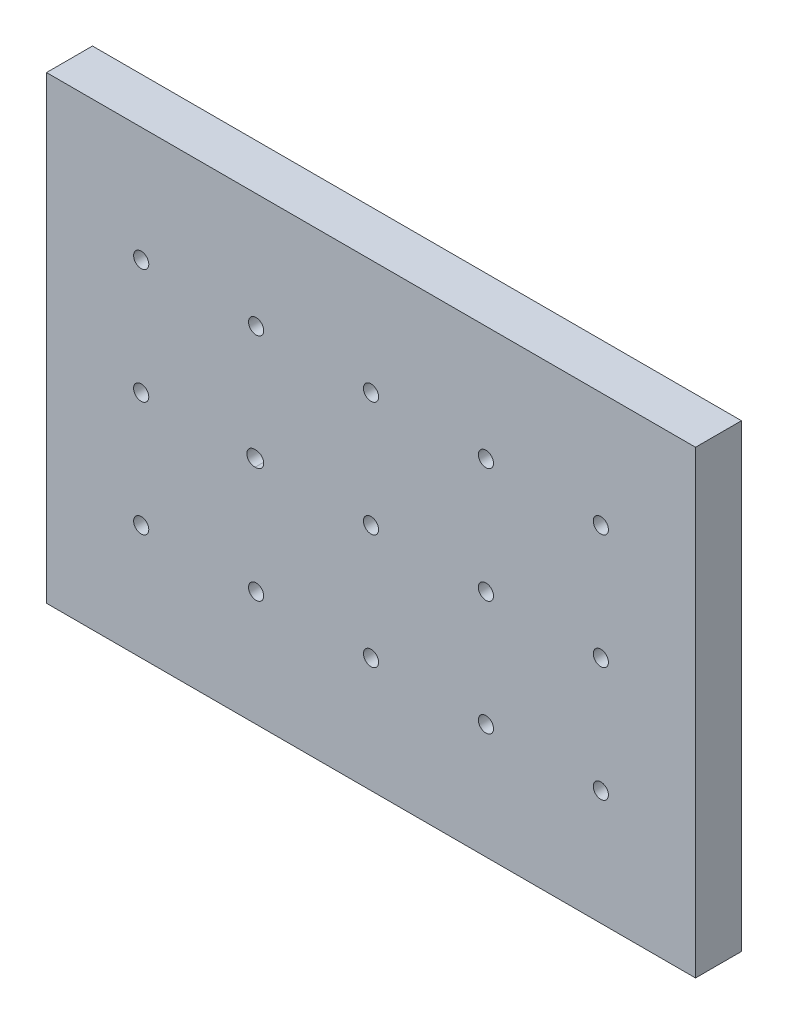
SolidWorks part; units mm, degrees
ref_plane "Front Plane" through (0, 0, 0) normal (0, 0, 1) x (1, 0, 0)
ref_plane "Top Plane" through (0, 0, 0) normal (0, 1, 0) x (1, 0, 0)
ref_plane "Right Plane" through (0, 0, 0) normal (1, 0, 0) x (0, 0, -1)
sketch "Sketch1" plane through (0, 0, 0) normal (0, 0, 1) x (1, 0, 0)
  line L1 (0, 0) -> (-141.2, 0)
  line L2 (0, 0) -> (0, 100)
  line L3 (0, 100) -> (-141.2, 100)
  line L4 (-141.2, 0) -> (-141.2, 100)
  dimension "D1" = 100
  dimension "D2" = 141.2
extrude "Boss-Extrude1" add sketch "Sketch1" along normal blind 10
hole_wizard "M4x0.7 Tapped Hole1" positions "Sketch2" profile "Sketch3" tap size "M4x0.7" standard "ANSI Metric" end condition through all
sketch "Sketch2" plane through (0, 0, 10) normal (0, 0, 1) x (1, 0, 0)
  line L0 (-141.2, 50) -> (0, 50) construction
  line L1 (-141.2, 100) -> (-141.2, 0) construction
  line L2 (0, 0) -> (0, 100) construction
  line L3 (-141.2, 100) -> (-141.2, 0) construction
  line L4 (-141.2, 62.5) -> (0, 62.5) construction
  line L6 (-141.2, 37.5) -> (0, 37.5) construction
  point P9 (-70.6, 50)
  point P10 (-95.6, 50)
  point P12 (-20.6, 50)
  point P14 (-45.6, 50)
  point P18 (-95.9728, 50)
  point P20 (-120.6, 50)
  point P43 (-20.6, 25)
  point P44 (-45.6, 25)
  point P45 (-70.6, 25)
  point P46 (-95.6, 25)
  point P47 (-120.6, 25)
  point P48 (-20.6, 75)
  point P49 (-45.6, 75)
  point P50 (-70.6, 75)
  point P51 (-95.6, 75)
  point P52 (-120.6, 75)
  dimension "D1" = 25
  dimension "D2" = 25
  dimension "D3" = 25
  dimension "D4" = 12.5
  dimension "D5" = 12.5
sketch "Sketch3" plane through (-120.6, 75, 10) normal (1, 0, 0) x (0, -1, 0)
  line L0 (0, 0) -> (0, 10)
  line L1 (0, 10) -> (1.65, 10)
  line L2 (1.65, 10) -> (1.65, 0)
  line L5 (1.65, 0) -> (0, 0)
  line L11 (0, -6.35) -> (0, 107.95) construction
  dimension "Thru Tap Drill Dia." = 3.3
  dimension "Thru Tap Drill Depth" = 10
cosmetic thread "Hole Thread1" parameters "D2"=4
cosmetic thread "Hole Thread2" parameters "D2"=4
cosmetic thread "Hole Thread3" parameters "D2"=4
cosmetic thread "Hole Thread4" parameters "D2"=4
cosmetic thread "Hole Thread5" parameters "D2"=4
cosmetic thread "Hole Thread6" parameters "D2"=4
cosmetic thread "Hole Thread7" parameters "D2"=4
cosmetic thread "Hole Thread8" parameters "D2"=4
cosmetic thread "Hole Thread9" parameters "D2"=4
cosmetic thread "Hole Thread10" parameters "D2"=4
cosmetic thread "Hole Thread11" parameters "D2"=4
cosmetic thread "Hole Thread12" parameters "D2"=4
cosmetic thread "Hole Thread13" parameters "D2"=4
cosmetic thread "Hole Thread14" parameters "D2"=4
cosmetic thread "Hole Thread15" parameters "D2"=4
cosmetic thread "Hole Thread16" parameters "D2"=4
